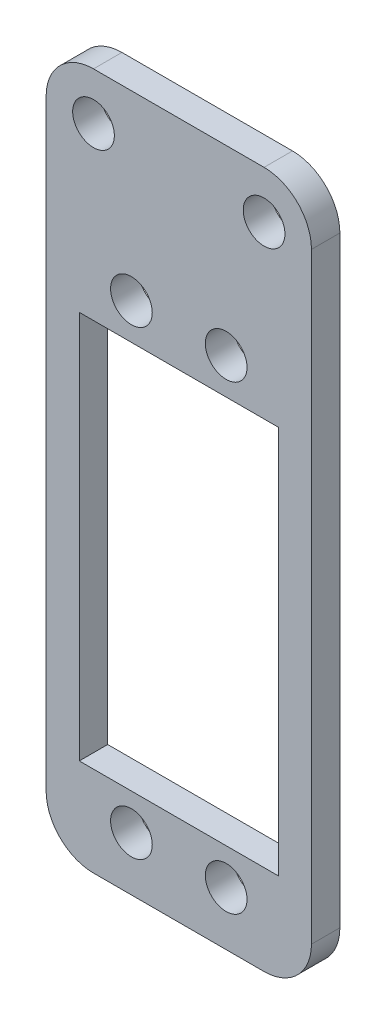
SolidWorks part; units mm, degrees
ref_plane "前视基准面" through (0, 0, 0) normal (0, 0, 1) x (1, 0, 0)
ref_plane "上视基准面" through (0, 0, 0) normal (0, 1, 0) x (1, 0, 0)
ref_plane "右视基准面" through (0, 0, 0) normal (1, 0, 0) x (0, 0, -1)
sketch "草图2" plane through (0, 0, 0) normal (0, 0, 1) x (1, 0, 0)
  line L0 (-9, -33.5) -> (9, -33.5)
  line L6 (-14, 35) -> (-14, -28.5)
  line L7 (14, 35) -> (14, -28.5)
  line L11 (-9, 40) -> (9, 40)
  arc A4 (-14, 35) -> (-9, 40) centre (-9, 35) cw
  arc A5 (14, 35) -> (9, 40) centre (9, 35) ccw
  arc A8 (-9, -33.5) -> (-14, -28.5) centre (-9, -28.5) cw
  arc A9 (9, -33.5) -> (14, -28.5) centre (9, -28.5) ccw
  point P0 (0, 0)
  point P6 (-14, 40)
  point P10 (14, 40)
  point P16 (-14, 3.25)
  dimension "D3" = 5
  dimension "D4" = 5
  dimension "D5" = 5
  dimension "D6" = 5
  dimension "D1" = 33.5
  dimension "D2" = 28
  dimension "D7" = 40
  dimension "D8" = 14
  dimension "D9" = 14
extrude "凸台-拉伸1" add sketch "草图2" along normal blind 3
sketch "草图3" plane through (0, 0, 3) normal (0, 0, 1) x (1, 0, 0)
  line L0 (0, 33.4196) -> (0, -3.5) construction
  line L1 (-10.5, -30.5) -> (10.5, -30.5)
  line L2 (-10.5, -30.5) -> (-10.5, 23.5)
  line L3 (-10.5, 23.5) -> (10.5, 23.5)
  line L4 (10.5, -30.5) -> (10.5, 23.5)
  line L5 (-10.5, -30.5) -> (10.5, 23.5) construction
  line L6 (-10.5, 23.5) -> (10.5, -30.5) construction
  line L7 (-9, -33.5) -> (9, -33.5) construction
  line L9 (-10.5, -3.5) -> (10.5, -3.5) construction
  line L10 (10.5, -24) -> (-10.5, -24)
  line L11 (10.5, -24) -> (10.5, 17)
  line L12 (10.5, 17) -> (-10.5, 17)
  line L13 (-10.5, -24) -> (-10.5, 17)
  line L14 (10.5, -24) -> (-10.5, 17) construction
  line L15 (10.5, 17) -> (-10.5, -24) construction
  line L17 (0, -3.5) -> (0, -38.2287) construction
  circle A0 centre (-5, -27.815) radius 2.2
  circle A3 centre (-5, 20.815) radius 2.2
  circle A4 centre (5, -27.815) radius 2.2
  circle A5 centre (5, 20.815) radius 2.2
  point P0 (0, -3.5)
  point P11 (0, -3.5)
  dimension "D5" = 4.4
  dimension "D1" = 54
  dimension "D2" = 21
  dimension "D3" = 57
  dimension "D4" = 41
  dimension "D6" = 5
  dimension "D7" = 48.63
extrude "切除-拉伸1" cut sketch "草图3" against normal through all contours A3 | A0 | L4 L12 L2 L10 | A4 | A5
sketch "草图4" plane through (0, 0, 3) normal (0, 0, 1) x (1, 0, 0)
  line L0 (14, -28.5) -> (14, 35) construction
  line L2 (-14, 35) -> (-14, -28.5) construction
  line L7 (9, 40) -> (-9, 40) construction
  circle A0 centre (-9, 35) radius 2.2
  circle A1 centre (9, 35) radius 2.2
  dimension "D1" = 4.4
  dimension "D2" = 4.4
  dimension "D3" = 5
  dimension "D4" = 5
  dimension "D5" = 5
  dimension "D6" = 5
extrude "切除-拉伸2" cut sketch "草图4" against normal through all
